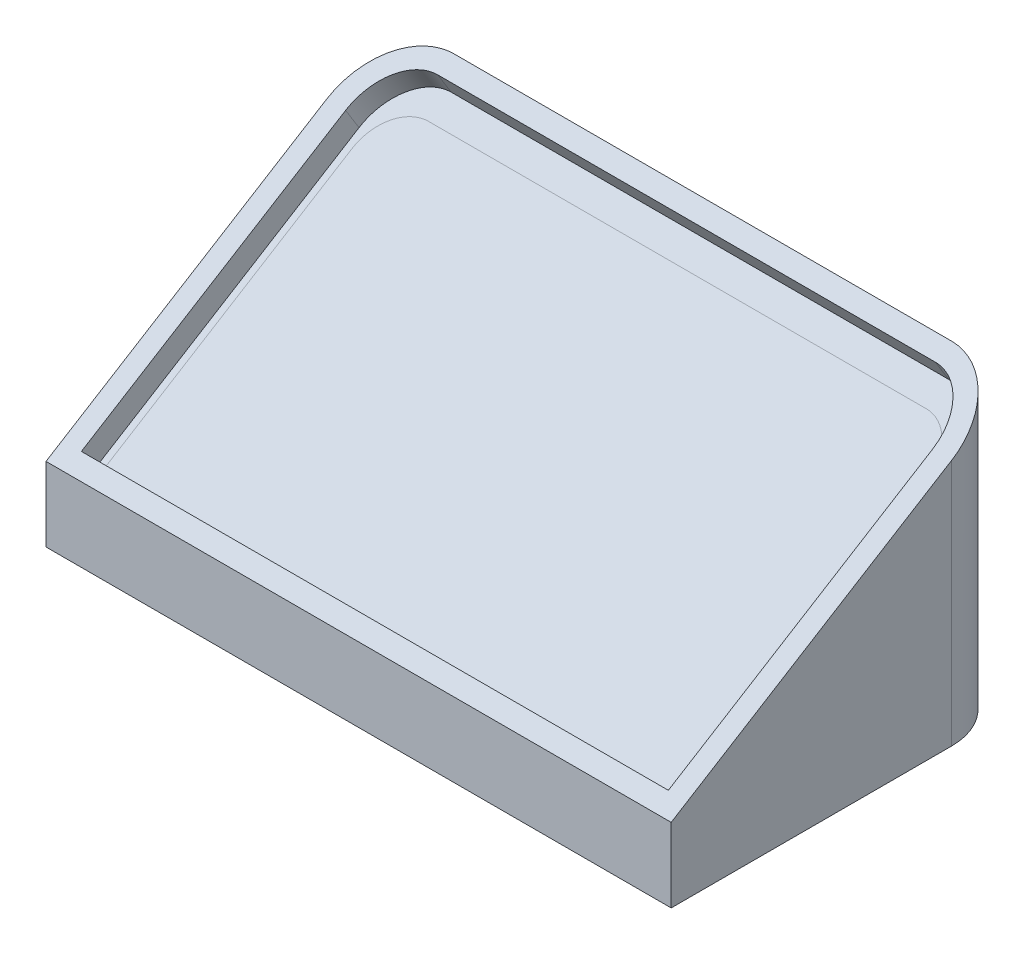
SolidWorks part; units mm, degrees
ref_plane "Front Plane" through (0, 0, 0) normal (0, 0, 1) x (1, 0, 0)
ref_plane "Top Plane" through (0, 0, 0) normal (0, 1, 0) x (1, 0, 0)
ref_plane "Right Plane" through (0, 0, 0) normal (1, 0, 0) x (0, 0, -1)
sketch "Sketch1" plane through (0, 0, 0) normal (0, 1, 0) x (1, 0, 0)
  line L1 (-67.5, 15) -> (67.5, 15)
  line L2 (-67.5, 15) -> (-67.5, -15)
  line L3 (-67.5, -15) -> (67.5, -15)
  line L4 (67.5, 15) -> (67.5, -15)
  line L5 (-67.5, 15) -> (67.5, -15) construction
  line L6 (-67.5, -15) -> (67.5, 15) construction
  point P0 (0, 0)
  dimension "D1" = 30
  dimension "D2" = 135
extrude "Boss-Extrude1" add sketch "Sketch1" along normal blind 2.5
sketch "Sketch2" plane through (0, 2.5, 0) normal (0, 1, 0) x (1, 0, 0)
  line L0 (-67.5, 12) -> (0, 14.8)
  line L1 (-67.5, 15) -> (-67.5, -15) construction
  line L2 (0, 14.8) -> (67.5, 12)
  line L3 (67.5, -15) -> (67.5, 15) construction
  line L4 (67.5, 12) -> (67.5, 15)
  line L5 (67.5, 15) -> (-67.5, 15) construction
  line L6 (67.5, 15) -> (-67.5, 15)
  line L7 (-67.5, 15) -> (-67.5, 12)
  dimension "D1" = 3
  dimension "D2" = 3
  dimension "D3" = 0.2
extrude "Cut-Extrude1" cut sketch "Sketch2" against normal through all
sketch "Sketch3" plane through (0, 2.5, 0) normal (0, 1, 0) x (1, 0, 0)
  line L0 (-67.5, -15) -> (67.5, -15) construction
  line L2 (62.5, -15) -> (62.5, 7)
  line L3 (59.5, 10) -> (20.4636, 10)
  line L4 (17.4636, -15) -> (17.4636, 7)
  line L5 (67.5, -15) -> (67.5, 12) construction
  line L6 (64.5, -15) -> (64.5, 7)
  line L7 (59.5, 12) -> (20.4636, 12)
  line L8 (15.4636, -15) -> (15.4636, 7)
  line L9 (62.5, -15) -> (64.5, -15)
  line L10 (17.4636, -15) -> (15.4636, -15)
  arc A0 (62.5, 7) -> (59.5, 10) centre (59.5, 7) ccw
  arc A1 (20.4636, 10) -> (17.4636, 7) centre (20.4636, 7) ccw
  arc A2 (64.5, 7) -> (59.5, 12) centre (59.5, 7) ccw
  arc A3 (20.4636, 12) -> (15.4636, 7) centre (20.4636, 7) ccw
  point P10 (62.5, 10)
  point P13 (17.4636, 10)
  dimension "D4" = 3
  dimension "D1" = 45.0364
  dimension "D2" = 25
  dimension "D3" = 5
  dimension "D5" = 2
extrude "Boss-Extrude2" add sketch "Sketch3" along normal blind 25
sketch "Sketch4" plane through (0, 2.5, 0) normal (0, 1, 0) x (1, 0, 0)
  line L4 (62.5, -15) -> (62.5, 7)
  line L5 (59.5, 10) -> (20.4636, 10)
  line L6 (17.4636, 7) -> (17.4636, -15)
  line L7 (17.4636, -15) -> (62.5, -15)
  line L8 (62.5, -15) -> (62.5, 7)
  line L9 (59.5, 10) -> (20.4636, 10)
  line L10 (17.4636, 7) -> (17.4636, -15)
  line L11 (17.4636, -15) -> (62.5, -15)
  arc A2 (62.5, 7) -> (59.5, 10) centre (59.5, 7) ccw
  arc A3 (20.4636, 10) -> (17.4636, 7) centre (20.4636, 7) ccw
  arc A4 (62.5, 7) -> (59.5, 10) centre (59.5, 7) ccw
  arc A5 (20.4636, 10) -> (17.4636, 7) centre (20.4636, 7) ccw
  dimension "D1" = 0
extrude "Cut-Extrude2" cut sketch "Sketch4" against normal through all
sketch "Sketch5" plane through (64.5, 0, 0) normal (1, 0, 0) x (0, 0, -1)
  line L0 (-15, 5.8158) -> (12, 22.5)
  line L1 (-15, 27.5) -> (-15, 2.5) construction
  line L2 (12, 27.5) -> (12, 2.5) construction
  line L3 (12, 22.5) -> (12, 27.5)
  line L4 (12, 27.5) -> (-15, 27.5)
  line L5 (-15, 27.5) -> (-15, 5.8158)
  dimension "D1" = 20
extrude "Cut-Extrude3" cut sketch "Sketch5" against normal through all
sketch "Sketch6" plane through (0, 10.9164, 6.7456) normal (0, 0.8507, 0.5257) x (1, 0, 0)
  line L0 (62.5, -9.7031) -> (62.5, 16.1582) construction
  line L1 (17.4636, 16.1582) -> (17.4636, -9.7031) construction
  line L2 (59.5, 19.6848) -> (20.4636, 19.6848) construction
  line L3 (62.5, -9.7031) -> (62.5, 16.1582)
  line L4 (17.4636, 16.1582) -> (17.4636, -9.7031)
  line L5 (59.5, 19.6848) -> (20.4636, 19.6848)
  line L6 (17.4636, -9.7031) -> (62.5, -9.7031)
  ellipse E0 centre (59.5, 16.1582) end of major axis (59.5, 12.6317) minor radius 3 (62.5, 16.1582) -> (59.5, 19.6848) ccw construction
  ellipse E1 centre (20.4636, 16.1582) end of major axis (20.4636, 12.6317) minor radius 3 (20.4636, 19.6848) -> (17.4636, 16.1582) ccw construction
  ellipse E2 centre (59.5, 16.1582) end of major axis (59.5, 12.6317) minor radius 3 (62.5, 16.1582) -> (59.5, 19.6848) ccw
  ellipse E3 centre (20.4636, 16.1582) end of major axis (20.4636, 12.6317) minor radius 3 (20.4636, 19.6848) -> (17.4636, 16.1582) ccw
extrude "Boss-Extrude3" add sketch "Sketch6" against normal blind 2
sketch "Sketch7" plane through (17.4636, 0, 0) normal (1, 0, 0) x (0, 0, -1)
  line L1 (-15, 5.8158) -> (-13, 5.8158)
  line L2 (-15, 5.8158) -> (-15, 0)
  line L3 (-15, 0) -> (-13, 0)
  line L4 (-13, 5.8158) -> (-13, 0)
  dimension "D1" = 2
extrude "Boss-Extrude4" add sketch "Sketch7" along normal up to surface (45.0364 mm away) up to face at (62.5, 5.3979, 5.9897)
sketch "Sketch8" plane through (0, 10.9164, 6.7456) normal (0, 0.8507, 0.5257) x (1, 0, 0)
  line L8 (16.9636, -8.2031) -> (63, -8.2031)
  line L9 (63, -8.2031) -> (63, 16.1582)
  line L10 (59.5, 20.5358) -> (20.4636, 20.5358)
  line L11 (16.9636, 16.1582) -> (16.9636, -8.2031)
  line L12 (16.9636, -8.2031) -> (63, -8.2031)
  line L13 (63, -8.2031) -> (63, 16.1582)
  line L14 (59.5, 20.5358) -> (20.4636, 20.5358)
  line L15 (16.9636, 16.1582) -> (16.9636, -8.2031)
  spline S0 degree 3 poles (4020.127, 464.7913) (-2604.7174, -683.8414) (90.9363, -76.5003) (62.7064, 17.9236) (62.6126, 18.1683) (62.3888, 18.6336) (62.2589, 18.8554) (61.959, 19.2753) (61.7874, 19.4745) (61.4121, 19.8285) (61.2073, 19.9855) (60.7573, 20.2514) (60.5208, 20.355) (43.1048, 25.3513) (-31.2875, -128.697) (3545.9468, -1930.2757) knots -47.560289 -47.560289 -47.560289 -47.560289 0.25 0.25 0.375 0.375 0.5 0.5 0.625 0.625 0.75 0.75 0.875 0.875 9.492959 9.492959 9.492959 9.492959 only from (63, 16.1582) to (59.5, 20.5358)
  spline S1 degree 3 poles (793.7815, -3903.3481) (131.7968, -313.721) (44.9024, 27.5824) (19.5753, 20.3934) (19.4519, 20.3492) (19.2144, 20.2465) (19.0996, 20.1879) (18.7662, 19.9921) (18.5572, 19.8332) (18.1812, 19.4799) (18.0114, 19.2839) (17.7089, 18.8622) (17.5784, 18.64) (17.3542, 18.1759) (17.2602, 17.9321) (17.1117, 17.4383) (17.0565, 17.1874) (13.5351, -7.0355) (171.4911, -74.2252) (944.3398, 3902.6754) knots -12.551964 -12.551964 -12.551964 -12.551964 0.125 0.125 0.1875 0.1875 0.25 0.25 0.375 0.375 0.5 0.5 0.625 0.625 0.75 0.75 0.875 0.875 12.631312 12.631312 12.631312 12.631312 only from (20.4636, 20.5358) to (16.9636, 16.1582)
  spline S2 degree 3 poles (63, 16.1582) (63, 16.6784) (62.9272, 17.1849) (62.7064, 17.9236) (62.6126, 18.1683) (62.3888, 18.6336) (62.2589, 18.8554) (61.959, 19.2753) (61.7874, 19.4745) (61.4121, 19.8285) (61.2073, 19.9855) (60.7573, 20.2514) (60.5208, 20.355) (60.0228, 20.4978) (59.7618, 20.5358) (59.5, 20.5358) knots 0 0 0 0 0.25 0.25 0.375 0.375 0.5 0.5 0.625 0.625 0.75 0.75 0.875 0.875 1 1 1 1
  spline S3 degree 3 poles (20.4636, 20.5358) (20.2026, 20.5358) (19.9481, 20.4992) (19.5753, 20.3934) (19.4519, 20.3492) (19.2144, 20.2465) (19.0996, 20.1879) (18.7662, 19.9921) (18.5572, 19.8332) (18.1812, 19.4799) (18.0114, 19.2839) (17.7089, 18.8622) (17.5784, 18.64) (17.3542, 18.1759) (17.2602, 17.9321) (17.1117, 17.4383) (17.0565, 17.1874) (16.9824, 16.6777) (16.9636, 16.4179) (16.9636, 16.1582) knots 0 0 0 0 0.125 0.125 0.1875 0.1875 0.25 0.25 0.375 0.375 0.5 0.5 0.625 0.625 0.75 0.75 0.875 0.875 1 1 1 1
  dimension "D1" = 1.5
extrude "Cut-Extrude4" cut sketch "Sketch8" against normal up to surface (2 mm away) up to face at (39.9818, 13.6857, -1.5404)
sketch "Sketch11" plane through (0, 0, 0) normal (0, -1, 0) x (1, 0, 0)
  line L5 (67.5, -12) -> (67.5, 15)
  line L6 (67.5, 15) -> (-67.5, 15)
  line L7 (-67.5, 15) -> (-67.5, -12)
  line L8 (-67.5, -12) -> (0, -14.8)
  line L9 (0, -14.8) -> (67.5, -12)
  line L10 (67.5, -12) -> (67.5, 15)
  line L11 (67.5, 15) -> (-67.5, 15)
  line L12 (-67.5, 15) -> (-67.5, -12)
  line L13 (-67.5, -12) -> (0, -14.8)
  line L14 (0, -14.8) -> (67.5, -12)
  dimension "D1" = 0
sketch "Sketch10" plane through (0, 9.2151, 5.6943) normal (0, 0.8507, 0.5257) x (1, 0, 0)
  line L0 (20.4636, 18.4489) -> (59.5, 18.4489) construction
  line L1 (20.4636, 18.4489) -> (59.5, 18.4489)
  line L2 (62.5, 14.9224) -> (62.5, -8.2031) construction
  line L3 (62.5, -8.2031) -> (17.4636, -8.2031) construction
  line L4 (17.4636, 14.9224) -> (17.4636, -8.2031) construction
  line L5 (62.5, 14.9224) -> (62.5, -8.2031)
  line L6 (62.5, -8.2031) -> (17.4636, -8.2031)
  line L7 (17.4636, 14.9224) -> (17.4636, -8.2031)
  ellipse E0 centre (59.5, 14.9224) end of major axis (59.5, 11.3958) minor radius 3 (62.5, 14.9224) -> (59.5, 18.4489) ccw construction
  ellipse E1 centre (20.4636, 14.9224) end of major axis (20.4636, 11.3958) minor radius 3 (20.4636, 18.4489) -> (17.4636, 14.9224) ccw construction
  ellipse E2 centre (59.5, 14.9224) end of major axis (59.5, 11.3958) minor radius 3 (62.5, 14.9224) -> (59.5, 18.4489) ccw
  ellipse E3 centre (20.4636, 14.9224) end of major axis (20.4636, 11.3958) minor radius 3 (20.4636, 18.4489) -> (17.4636, 14.9224) ccw
extrude "Boss-Extrude6" add sketch "Sketch10" against normal blind 2 separate body
sketch "Sketch12" plane through (0, 0, 0) normal (0, -1, 0) x (1, 0, 0)
  line L3 (62.5, 13) -> (17.4636, 13) construction
  line L6 (62.5, 13) -> (62.5, -7) construction
  line L7 (59.5, -10) -> (20.4636, -10) construction
  line L8 (17.4636, -7) -> (17.4636, 13) construction
  line L9 (62.5, 13) -> (17.4636, 13)
  line L10 (62.5, 13) -> (62.5, -7)
  line L11 (59.5, -10) -> (20.4636, -10)
  line L12 (17.4636, -7) -> (17.4636, 13)
  arc A0 (59.5, -10) -> (62.5, -7) centre (59.5, -7) ccw construction
  arc A1 (17.4636, -7) -> (20.4636, -10) centre (20.4636, -7) ccw construction
  arc A2 (59.5, -10) -> (62.5, -7) centre (59.5, -7) ccw
  arc A3 (17.4636, -7) -> (20.4636, -10) centre (20.4636, -7) ccw
extrude "Boss-Extrude8" add sketch "Sketch12" against normal up to surface (2.3496 mm away) separate body
sketch "Sketch13" plane through (0, 2.5, 0) normal (0, 1, 0) x (1, 0, 0)
  line L9 (15.4636, -15) -> (15.4636, 7)
  line L10 (20.4636, 12) -> (59.5, 12)
  line L11 (64.5, 7) -> (64.5, -15)
  line L12 (64.5, -15) -> (67.5, -15)
  line L13 (67.5, -15) -> (67.5, 12)
  line L14 (67.5, 12) -> (0, 14.8)
  line L15 (0, 14.8) -> (-67.5, 12)
  line L16 (-67.5, 12) -> (-67.5, -15)
  line L17 (-67.5, -15) -> (15.4636, -15)
  line L18 (15.4636, -15) -> (15.4636, 7)
  line L19 (20.4636, 12) -> (59.5, 12)
  line L20 (64.5, 7) -> (64.5, -15)
  line L21 (64.5, -15) -> (67.5, -15)
  line L22 (67.5, -15) -> (67.5, 12)
  line L23 (67.5, 12) -> (0, 14.8)
  line L24 (0, 14.8) -> (-67.5, 12)
  line L25 (-67.5, 12) -> (-67.5, -15)
  line L26 (-67.5, -15) -> (15.4636, -15)
  arc A2 (20.4636, 12) -> (15.4636, 7) centre (20.4636, 7) ccw
  arc A3 (64.5, 7) -> (59.5, 12) centre (59.5, 7) ccw
  arc A4 (20.4636, 12) -> (15.4636, 7) centre (20.4636, 7) ccw
  arc A5 (64.5, 7) -> (59.5, 12) centre (59.5, 7) ccw
  dimension "D1" = 0
extrude "Cut-Extrude5" cut sketch "Sketch13" against normal blind 10
